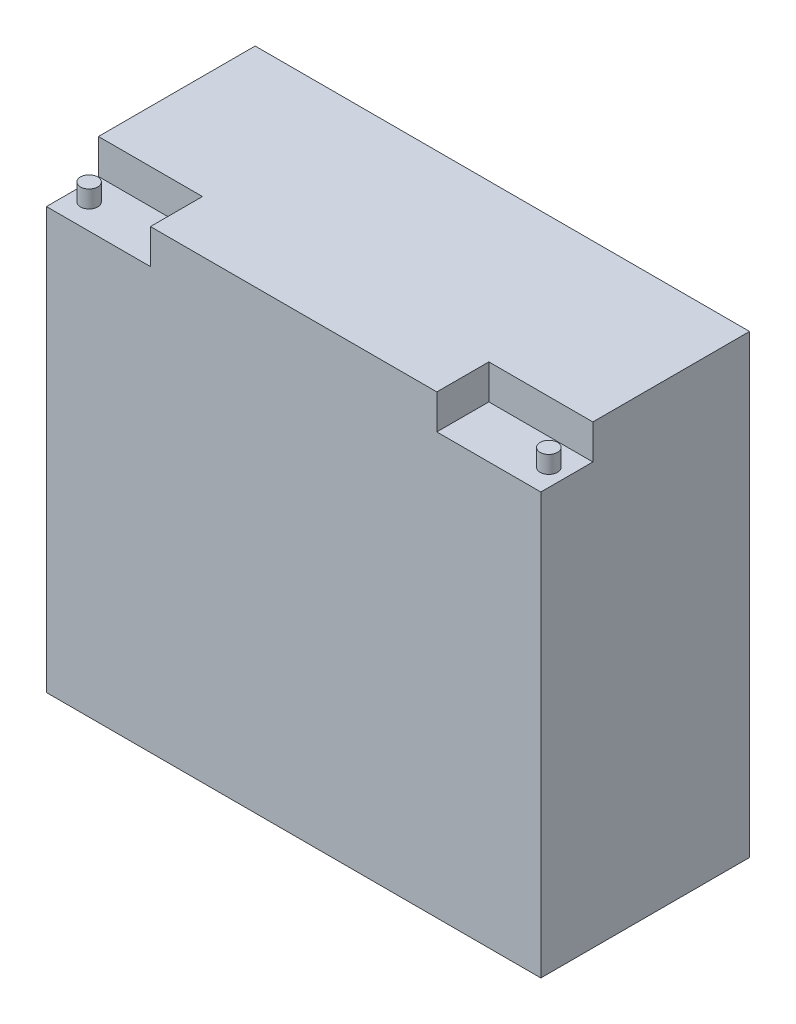
SolidWorks part; units mm, degrees
ref_plane "Front" through (0, 0, 0) normal (0, 0, 1) x (1, 0, 0)
ref_plane "Top" through (0, 0, 0) normal (0, 1, 0) x (1, 0, 0)
ref_plane "Right" through (0, 0, 0) normal (1, 0, 0) x (0, 0, -1)
sketch "Sketch1" plane through (0, 0, 0) normal (0, 1, 0) x (1, 0, 0)
  line L1 (-111.2738, -8.2618) -> (69.8282, -8.2618)
  line L2 (-111.2738, -8.2618) -> (-111.2738, -84.7158)
  line L3 (-111.2738, -84.7158) -> (69.8282, -84.7158)
  line L4 (69.8282, -8.2618) -> (69.8282, -84.7158)
  dimension "D1" = 76.454
  dimension "D2" = 181.102
extrude "Boss-Extrude1" add sketch "Sketch1" along normal blind 166.878
sketch "Sketch2" plane through (0, 166.878, 0) normal (0, 1, 0) x (1, 0, 0)
  line L0 (-111.2738, -8.2618) -> (-111.2738, -84.7158) construction
  line L1 (-111.2738, -65.6658) -> (-73.1738, -65.6658)
  line L2 (-111.2738, -65.6658) -> (-111.2738, -84.7158)
  line L3 (-111.2738, -84.7158) -> (-73.1738, -84.7158)
  line L4 (-73.1738, -65.6658) -> (-73.1738, -84.7158)
  line L6 (69.8282, -84.7158) -> (31.7282, -84.7158)
  line L7 (69.8282, -84.7158) -> (69.8282, -65.6658)
  line L8 (69.8282, -65.6658) -> (31.7282, -65.6658)
  line L9 (31.7282, -84.7158) -> (31.7282, -65.6658)
  dimension "D1" = 38.1
  dimension "D2" = 38.1
  dimension "D3" = 19.05
  dimension "D4" = 19.05
extrude "Cut-Extrude1" cut sketch "Sketch2" against normal blind 12.7
sketch "Sketch3" plane through (0, 154.178, 0) normal (0, 1, 0) x (1, 0, 0)
  line L0 (-111.2738, -65.6658) -> (-111.2738, -84.7158) construction
  line L1 (69.8282, -84.7158) -> (69.8282, -65.6658) construction
  circle A0 centre (63.4782, -75.4438) radius 3.175
  circle A1 centre (-104.9238, -75.4438) radius 3.175
  dimension "D2" = 6.35
  dimension "D3" = 6.35
  dimension "D1" = 6.35
  dimension "D4" = 6.35
extrude "Boss-Extrude2" add sketch "Sketch3" along normal blind 6.35
